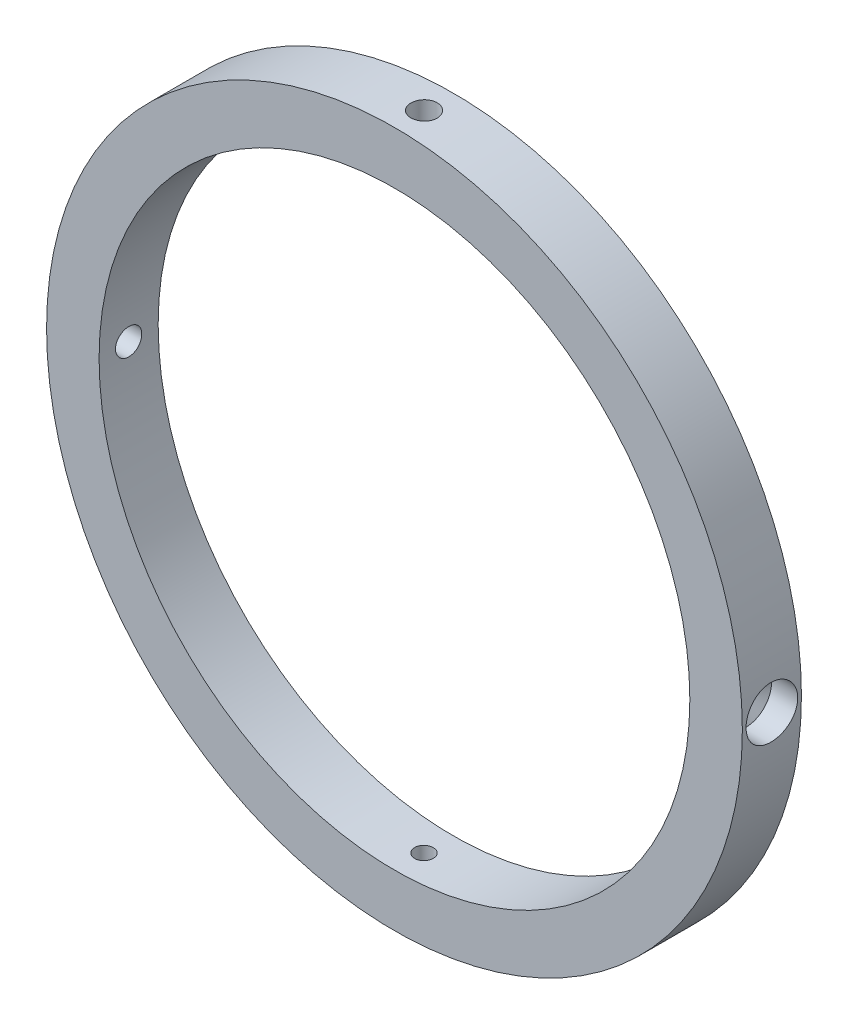
SolidWorks part; units mm, degrees
material "6061-T6 (SS)"
ref_plane "Front Plane" through (0, 0, 0) normal (0, 0, 1) x (1, 0, 0)
ref_plane "Top Plane" through (0, 0, 0) normal (0, 1, 0) x (1, 0, 0)
ref_plane "Right Plane" through (0, 0, 0) normal (1, 0, 0) x (0, 0, -1)
sketch "Sketch1" plane through (0, 0, 0) normal (0, 0, 1) x (1, 0, 0)
  circle A0 centre (0, 0) radius 42.0688
  circle A1 centre (0, 0) radius 35.7188
  dimension "D1" = 84.1375
  dimension "D2" = 6.35
extrude "Boss-Extrude1" add sketch "Sketch1" along normal mid plane 7.1437
hole_wizard "Hole1" positions "3DSketch1" profile "Sketch2" legacy
sketch3d "3DSketch1"
  point P0 (0, 42.0688, 0)
sketch "Sketch2" plane through (0, 42.0688, 0) normal (1, 0, 0) x (0, 0, 1)
  line L0 (0, 0) -> (0, 2.3813)
  line L1 (0, 2.3813) -> (1.5875, 2.3813)
  line L2 (1.5875, 2.3813) -> (1.5875, 0)
  line L3 (1.5875, 0) -> (0, 0)
  line L4 (0, 110) -> (0, -10) construction
  dimension "Diameter" = 3.175
  dimension "Depth" = 2.3813
hole_wizard "#4-40 Tapped Hole1" positions "Sketch5" profile "Sketch7" tap size "#4-40" standard "ANSI Inch"
sketch "Sketch5" plane through (0, 39.6875, 0) normal (0, 1, 0) x (1, 0, 0)
  point P0 (0, 0)
cosmetic thread "Hole Thread1" parameters "D1"=4.0023, "D2"=2.8448
sketch "Sketch7" plane through (0, 39.6875, 0) normal (1, 0, 0) x (0, 0, 1)
  line L0 (0, 0) -> (0, 8.2992)
  line L1 (0, 8.2992) -> (1.1303, 7.62)
  line L2 (1.1303, 7.62) -> (1.1303, 0)
  line L5 (1.1303, 0) -> (0, 0)
  line L10 (0, 8.2992) -> (-1.1303, 7.62) construction
  line L11 (0, -6.35) -> (0, 107.95) construction
  dimension "Tap Drill Dia." = 2.2606
  dimension "Tap Drill Depth" = 7.62
  dimension "Drill Angle" = 118
hole_wizard "Hole2" positions "3DSketch2" profile "Sketch8" legacy
sketch3d "3DSketch2"
  point P0 (-42.0688, 0, 0)
  point P3 (0, 0, 0)
sketch "Sketch8" plane through (-42.0688, 0, 0) normal (0, 1, 0) x (0, 0, 1)
  line L0 (0, 0) -> (0, 12.7)
  line L1 (0, 12.7) -> (1.5875, 12.7)
  line L2 (1.5875, 12.7) -> (1.5875, 4.0983)
  line L3 (1.5875, 4.0983) -> (3.1242, 3.175)
  line L4 (3.1242, 3.175) -> (3.1242, 0)
  line L5 (3.1242, 0) -> (0, 0)
  line L6 (0, -6.13) -> (0, 109.2824) construction
  line L7 (-1.5875, 4.0983) -> (-3.1242, 3.175) construction
  line L8 (0, 12.7) -> (-1.5875, 12.7) construction
  dimension "Diameter" = 3.175
  dimension "Depth" = 12.7
  dimension "C-Drill Diameter" = 6.2484
  dimension "C-Drill Depth" = 3.175
  dimension "C-Drill Angle" = 118
pattern_circular "CirPattern1" count 2 over 360 about axis through (0, 0, 3.5719) along (0, 0, -1) of "Hole1", "#4-40 Tapped Hole1", "Hole2"
